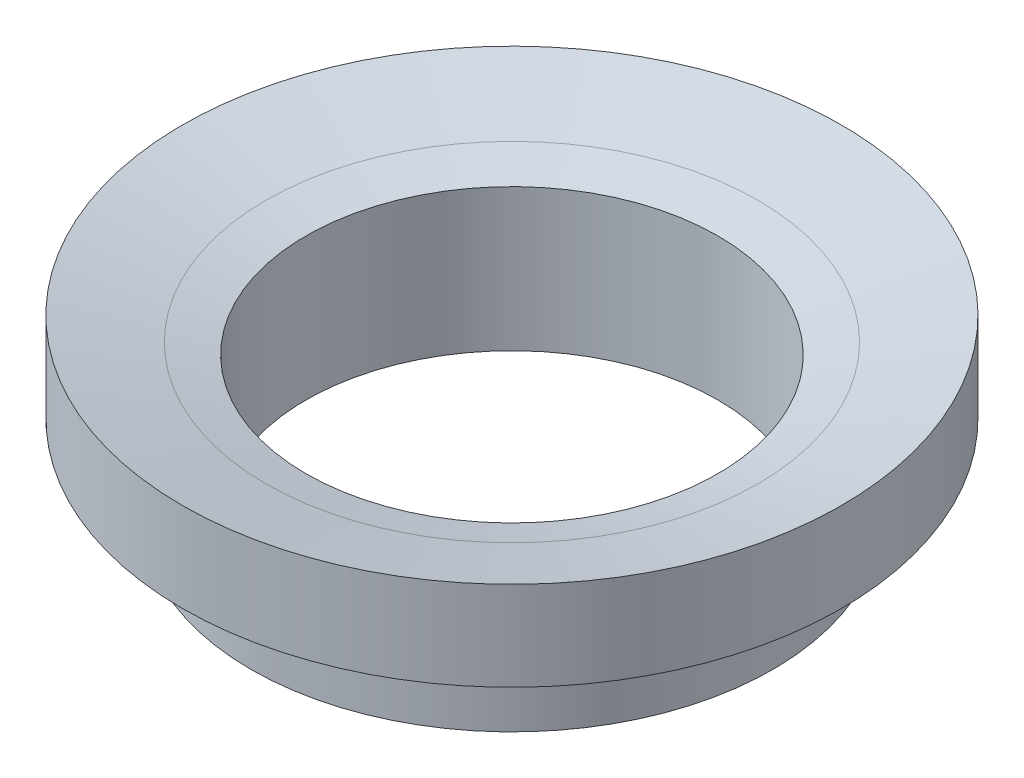
SolidWorks part; units mm, degrees
material "Ceramic Porcelain"
ref_plane "Front Plane" through (0, 0, 0) normal (0, 0, 1) x (1, 0, 0)
ref_plane "Top Plane" through (0, 0, 0) normal (0, 1, 0) x (1, 0, 0)
ref_plane "Right Plane" through (0, 0, 0) normal (1, 0, 0) x (0, 0, -1)
curve "Curve1"
  spline degree 3 poles (0, 0, 15) (0, 0.0092, 15.0333) (0, 0.0276, 15.1) (0, 0.0553, 15.2) (0, 0.0829, 15.3) (0, 0.1106, 15.4) (0, 0.1382, 15.5) (0, 0.1659, 15.6) (0, 0.1935, 15.7) (0, 0.2212, 15.8) (0, 0.2488, 15.9) (0, 0.2765, 16) (0, 0.3041, 16.1) (0, 0.3318, 16.2) (0, 0.3594, 16.3) (0, 0.3871, 16.4) (0, 0.4147, 16.5) (0, 0.4424, 16.6) (0, 0.47, 16.7) (0, 0.4976, 16.8) (0, 0.5253, 16.9) (0, 0.5529, 17) (0, 0.5806, 17.1) (0, 0.6082, 17.2) (0, 0.6359, 17.3) (0, 0.6635, 17.4) (0, 0.6912, 17.5) (0, 0.7188, 17.6) (0, 0.7465, 17.7) (0, 0.7741, 17.8) (0, 0.7926, 17.8667) (0, 0.8018, 17.9) knots 0 0 0 0 0.034478 0.068966 0.103444 0.137932 0.17241 0.206897 0.241376 0.275863 0.310342 0.344829 0.379308 0.413795 0.448273 0.482761 0.517239 0.551727 0.586205 0.620684 0.655171 0.689649 0.724137 0.758615 0.793103 0.827581 0.862068 0.896547 0.931034 0.965513 1 1 1 1
sketch "Sketch1" plane through (0, 0, 0) normal (1, 0, 0) x (0, 0, -1)
  line L0 (-15, 0) -> (-15, -10.35)
  line L1 (-15, -10.35) -> (-19, -10.35)
  line L2 (-19, -10.35) -> (-19, -4)
  line L3 (-19, -4) -> (-24, -4)
  line L4 (-17.9, 0.8018) -> (-24, 2.4937)
  line L5 (-24, 2.4937) -> (-24, -4)
  line L6 (0, 0) -> (0, -5.9247)
  spline S0 degree 3 poles (-509.4291, -1937.7043) (11.9658, -2.0337) (-2.3012, -3.5283) (-15.2, 0.0553) (-15.3, 0.0829) (-15.4, 0.1106) (-15.5, 0.1382) (-15.6, 0.1659) (-15.7, 0.1935) (-15.8, 0.2212) (-15.9, 0.2488) (-16, 0.2765) (-16.1, 0.3041) (-16.2, 0.3318) (-16.3, 0.3594) (-16.4, 0.3871) (-16.5, 0.4147) (-16.6, 0.4424) (-16.7, 0.47) (-16.8, 0.4976) (-16.9, 0.5253) (-17, 0.5529) (-17.1, 0.5806) (-17.2, 0.6082) (-17.3, 0.6359) (-17.4, 0.6635) (-17.5, 0.6912) (-17.6, 0.7188) (-17.7, 0.7465) (-30.609, 4.2987) (-42.0828, 12.9114) (-589.1447, -1915.6333) knots -13.244731 -13.244731 -13.244731 -13.244731 0.034478 0.068966 0.103444 0.137932 0.17241 0.206897 0.241376 0.275863 0.310342 0.344829 0.379308 0.413795 0.448273 0.482761 0.517239 0.551727 0.586205 0.620684 0.655171 0.689649 0.724137 0.758615 0.793103 0.827581 0.862068 0.896547 0.931034 0.965513 14.246165 14.246165 14.246165 14.246165 only from (-15, 0) to (-17.9, 0.8018) construction
  spline S1 degree 3 poles (-15, 0) (-15.0333, 0.0092) (-15.1, 0.0276) (-15.2, 0.0553) (-15.3, 0.0829) (-15.4, 0.1106) (-15.5, 0.1382) (-15.6, 0.1659) (-15.7, 0.1935) (-15.8, 0.2212) (-15.9, 0.2488) (-16, 0.2765) (-16.1, 0.3041) (-16.2, 0.3318) (-16.3, 0.3594) (-16.4, 0.3871) (-16.5, 0.4147) (-16.6, 0.4424) (-16.7, 0.47) (-16.8, 0.4976) (-16.9, 0.5253) (-17, 0.5529) (-17.1, 0.5806) (-17.2, 0.6082) (-17.3, 0.6359) (-17.4, 0.6635) (-17.5, 0.6912) (-17.6, 0.7188) (-17.7, 0.7465) (-17.8, 0.7741) (-17.8667, 0.7926) (-17.9, 0.8018) knots 0 0 0 0 0.034478 0.068966 0.103444 0.137932 0.17241 0.206897 0.241376 0.275863 0.310342 0.344829 0.379308 0.413795 0.448273 0.482761 0.517239 0.551727 0.586205 0.620684 0.655171 0.689649 0.724137 0.758615 0.793103 0.827581 0.862068 0.896547 0.931034 0.965513 1 1 1 1
  dimension "D1" = 24
  dimension "D2" = 4
  dimension "D3" = 19
  dimension "D4" = 6.35
revolve "Revolve1" add sketch "Sketch1" angle 360 about L6
equation "\"r_cc_inner\"= 10'combustion chamber inner radius [mm]"
equation "\"r_cc_outer\"= 24'combustion chamber outer radius [mm]"
equation "\"L_star\"= 1500'combustion process characteristic length [mm]"
equation "\"At\"= 0.0000598 * ( 1000 ) ^ 2'Throat Area [mm^2]"
equation "\"x_cc\"= \"L_star\" * \"At\" / ( pi * ( \"r_cc_outer\" ^ 2 - \"r_cc_inner\" ^ 2 ) )'combustion chamber physical length [mm]"
equation "\"x_convergent\"= 20'length of the convergent section of the nozzle [mm]"
equation "\"r_throat\"= 15'outer radius of throat gap [mm]"
equation "\"x_material_change\"= 1.5 * \"r_throat\"'distance below throat at which nozzle material changes to a low-temp material [mm]"
equation "\"t_i\"= 8'insulation thickness required by thermal considerations [mm]"
equation "\"t_cw\"= 4'pressure vessle cylinder wall thickness required by structural considerations [mm]"
equation "\"t_p\" = 1 / 4 * 25.4'pressure vessle plate thickness required by structural considerations [mm]"
equation "\"r_outer\"= \"r_cc_outer\" + \"t_i\" + \"t_cw\" + 10'overall outermost radius of engine [mm]"
equation "\"D1@Sketch1\"=\"r_cc_outer\""
equation "\"D2@Sketch1\"=\"t_i\"/2"
equation "\"r_rod\"= 1 / 8 * 25.4 / 2'radius of the threaded rod in the center fo the spike [mm]"
equation "\"D3@Sketch1\"=\"t_i\"/2 + \"r_throat\""
equation "\"D4@Sketch1\"=\"t_p\""
